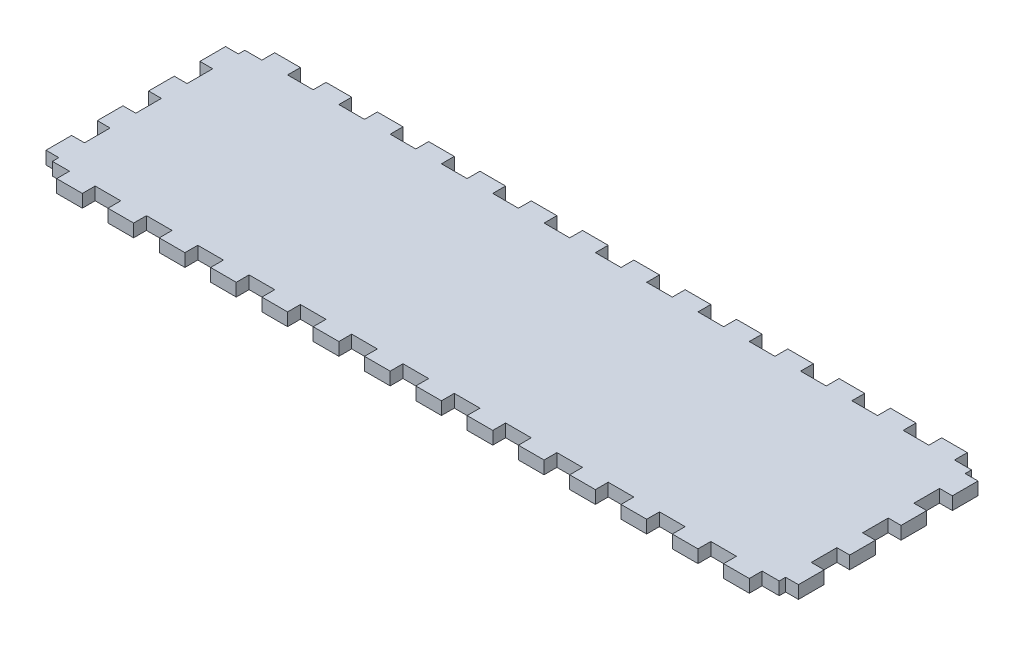
SolidWorks part; units mm, degrees
ref_plane "Front Plane" through (0, 0, 0) normal (0, 0, 1) x (1, 0, 0)
ref_plane "Top Plane" through (0, 0, 0) normal (0, 1, 0) x (1, 0, 0)
ref_plane "Right Plane" through (0, 0, 0) normal (1, 0, 0) x (0, 0, -1)
sketch "Sketch1" plane through (0, 0, 0) normal (0, 1, 0) x (1, 0, 0)
  line L1 (-85, 22.5) -> (85, 22.5)
  line L2 (-85, 22.5) -> (-85, -22.5)
  line L3 (-85, -22.5) -> (85, -22.5)
  line L4 (85, 22.5) -> (85, -22.5)
  line L5 (-85, 22.5) -> (85, -22.5) construction
  line L6 (-85, -22.5) -> (85, 22.5) construction
  point P0 (0, 0)
  dimension "D1" = 45
  dimension "D2" = 170
extrude "Boss-Extrude1" add sketch "Sketch1" along normal blind 3
sketch "Sketch2" plane through (0, 0, 22.5) normal (0, 0, 1) x (1, 0, 0)
  line L0 (0, 0) -> (0, 3) construction
  line L1 (-85, 0) -> (85, 0) construction
  line L2 (-85, 3) -> (85, 3) construction
  line L4 (3, 0) -> (9, 0)
  line L5 (3, 0) -> (3, 3)
  line L6 (3, 3) -> (9, 3)
  line L7 (9, 0) -> (9, 3)
  line L8 (3, 0) -> (9, 3) construction
  line L9 (3, 3) -> (9, 0) construction
  point P10 (6, 1.5)
  dimension "D1" = 3
  dimension "D2" = 6
extrude "Boss-Extrude2" add sketch "Sketch2" along normal blind 3
pattern_linear "LPattern1" count 7 spacing 12 along (1, 0, 0) count 8 spacing 12 along (-1, 0, 0) of "Boss-Extrude2"
sketch "Sketch3" plane through (85, 0, 0) normal (1, 0, 0) x (0, 0, -1)
  line L0 (0, 3) -> (0, 0) construction
  line L1 (-22.5, 3) -> (22.5, 3) construction
  line L2 (-22.5, 0) -> (22.5, 0) construction
  line L4 (3, 3) -> (9, 3)
  line L5 (3, 3) -> (3, 0)
  line L6 (3, 0) -> (9, 0)
  line L7 (9, 3) -> (9, 0)
  line L8 (3, 3) -> (9, 0) construction
  line L9 (3, 0) -> (9, 3) construction
  point P10 (6, 1.5)
  dimension "D1" = 6
  dimension "D2" = 3
extrude "Boss-Extrude3" add sketch "Sketch3" along normal blind 3
pattern_linear "LPattern2" count 2 spacing 12 along (0, 0, -1) count 3 spacing 12 along (0, 0, 1) of "Boss-Extrude3"
ref_plane "Plane1" through (0, 0, 0) normal (-1, 0, 0) x (0, 0, 1)
ref_plane "Plane2" through (0, 0, 0) normal (0, 0, -1) x (-1, 0, 0)
mirror "Mirror1" about plane through (0, 0, 0) normal (0, 0, -1) of "LPattern1", "Boss-Extrude2"
mirror "Mirror2" about plane through (0, 0, 0) normal (-1, 0, 0) of "LPattern2", "Boss-Extrude3"
